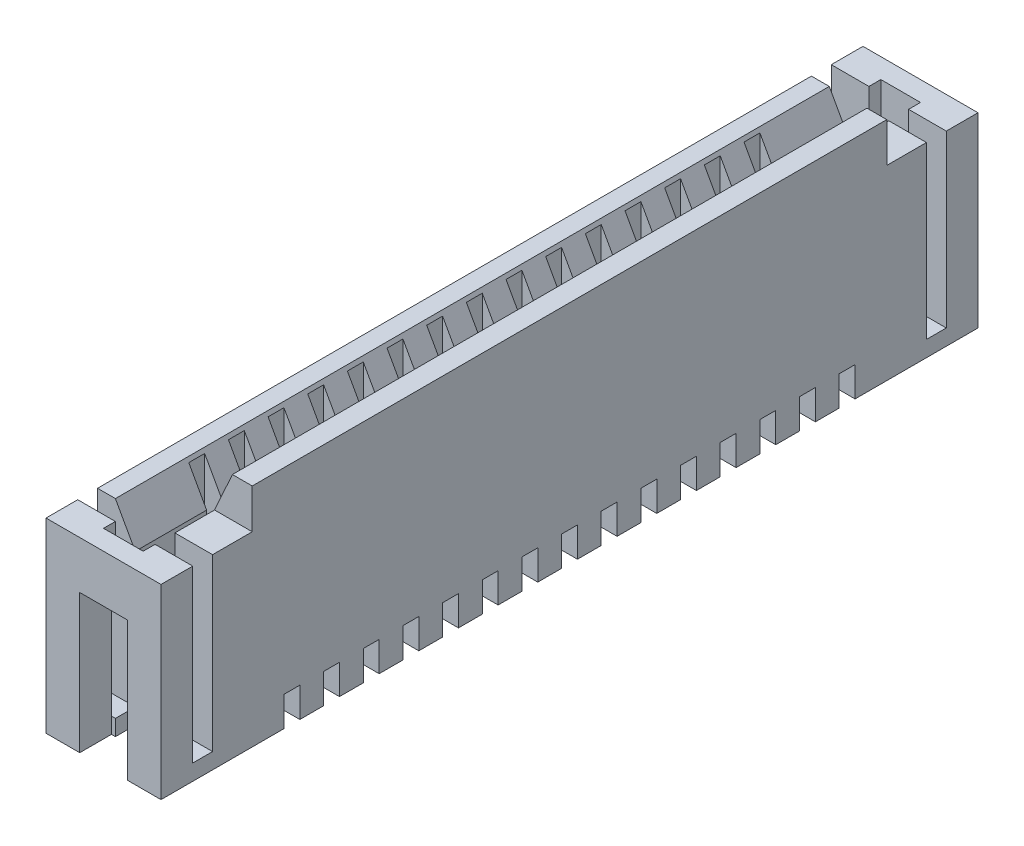
SolidWorks part; units mm, degrees
ref_plane "Plano frontal" through (0, 0, 0) normal (0, 0, 1) x (1, 0, 0)
ref_plane "Plano superior" through (0, 0, 0) normal (0, 1, 0) x (1, 0, 0)
ref_plane "Plano direito" through (0, 0, 0) normal (1, 0, 0) x (0, 0, -1)
sketch "Esboço1" plane through (0, 0, 0) normal (0, 1, 0) x (1, 0, 0)
  line L1 (-1.45, -10.3) -> (1.45, -10.3)
  line L2 (-1.45, -10.3) -> (-1.45, 10.3)
  line L3 (-1.45, 10.3) -> (1.45, 10.3)
  line L4 (1.45, -10.3) -> (1.45, 10.3)
  line L5 (-1.45, -10.3) -> (1.45, 10.3) construction
  line L6 (-1.45, 10.3) -> (1.45, -10.3) construction
  point P0 (0, 0)
  dimension "D1" = 20.6
  dimension "D2" = 2.9
extrude "Ressalto-extrusão1" add sketch "Esboço1" along normal blind 4.7
sketch "Esboço2" plane through (0, 4.7, 0) normal (0, 1, 0) x (1, 0, 0)
  line L1 (-0.5, -9.8) -> (0.5, -9.8)
  line L2 (-0.5, -9.8) -> (-0.5, 9.8)
  line L3 (-0.5, 9.8) -> (0.5, 9.8)
  line L4 (0.5, -9.8) -> (0.5, 9.8)
  line L5 (-0.5, -9.8) -> (0.5, 9.8) construction
  line L6 (-0.5, 9.8) -> (0.5, -9.8) construction
  point P0 (0, 0)
  dimension "D1" = 19.6
  dimension "D2" = 1
extrude "Corte-extrusão1" cut sketch "Esboço2" against normal blind 4.3
sketch "Esboço3" plane through (0, 4.7, 0) normal (0, 1, 0) x (1, 0, 0)
  line L1 (-3.2854, 9.5) -> (3.6069, 9.5)
  line L2 (-3.2854, 9.5) -> (-3.2854, 9)
  line L3 (-3.2854, 9) -> (3.6069, 9)
  line L4 (3.6069, 9.5) -> (3.6069, 9)
  line L5 (-3.2854, -9) -> (4.0468, -9)
  line L6 (-3.2854, -9) -> (-3.2854, -9.5)
  line L7 (-3.2854, -9.5) -> (4.0468, -9.5)
  line L8 (4.0468, -9) -> (4.0468, -9.5)
  dimension "D1" = 9
  dimension "D2" = 9
  dimension "D3" = 0.5
  dimension "D4" = 0.5
extrude "Corte-extrusão2" cut sketch "Esboço3" against normal blind 4.3
chamfer "Chanfro2" distance 0.5 angle 61 1 edges at (-0.5, 4.7, 0)
sketch "Esboço4" plane through (0, 0, 0) normal (0, 0, 1) x (1, 0, 0)
  line L0 (1.45, 4.7) -> (1.45, 5.7)
  line L1 (1.45, 5.7) -> (0.95, 5.7)
  line L2 (0.95, 5.7) -> (0.5, 4.7)
  line L3 (-1.45, 4.7) -> (1.45, 4.7) construction
  line L4 (0.5, 4.7) -> (1.45, 4.7)
  dimension "D1" = 0.95
  dimension "D2" = 1
  dimension "D3" = 0.5
extrude "Ressalto-extrusão2" add sketch "Esboço4" along normal mid plane 16
sketch "Esboço5" plane through (0, 0.4, 0) normal (0, 1, 0) x (1, 0, 0)
  line L0 (0.5, -9) -> (0.5, 9) construction
  line L1 (-0.5, 9.8) -> (0.5, 9.8)
  line L2 (-0.5, 9.8) -> (-0.5, 8.7)
  line L3 (-0.5, 8.7) -> (0.5, 8.7)
  line L4 (0.5, 9.8) -> (0.5, 8.7)
  line L5 (-0.5, 9) -> (-0.5, -9) construction
  line L6 (0.5, -9.8) -> (-0.5, -9.8)
  line L7 (0.5, -9.8) -> (0.5, -8.7)
  line L8 (0.5, -8.7) -> (-0.5, -8.7)
  line L9 (-0.5, -9.8) -> (-0.5, -8.7)
  dimension "D1" = 1.1
  dimension "D2" = 1.1
extrude "Corte-extrusão3" cut sketch "Esboço5" against normal blind 2
sketch "Esboço6" plane through (0, 0.4, 0) normal (0, 1, 0) x (1, 0, 0)
  line L0 (0.5, -8.7) -> (0.5, 8.7) construction
  line L1 (-0.5, 8.7) -> (0.5, 8.7)
  line L2 (-0.5, 8.7) -> (-0.5, 8.3)
  line L3 (-0.5, 8.3) -> (0.5, 8.3)
  line L4 (0.5, 8.7) -> (0.5, 8.3)
  line L5 (-0.5, 8.7) -> (-0.5, -8.7) construction
  line L6 (0.5, -8.7) -> (-0.5, -8.7)
  line L7 (0.5, -8.7) -> (0.5, -8.3)
  line L8 (0.5, -8.3) -> (-0.5, -8.3)
  line L9 (-0.5, -8.7) -> (-0.5, -8.3)
  dimension "D1" = 0.4
  dimension "D2" = 0.4
extrude "Ressalto-extrusão3" add sketch "Esboço6" along normal blind 2
sketch "Esboço7" plane through (0, 4.7, 0) normal (0, 1, 0) x (1, 0, 0)
  line L0 (-1.45, 9) -> (-1.45, -9) construction
  line L1 (-0.95, 0.2) -> (-0.25, 0.2)
  line L2 (-0.95, 0.2) -> (-0.95, -0.2)
  line L3 (-0.95, -0.2) -> (-0.25, -0.2)
  line L4 (-0.25, 0.2) -> (-0.25, -0.2)
  line L5 (1.45, -8) -> (1.45, 8) construction
  line L6 (0.25, 0.2) -> (0.95, 0.2)
  line L7 (0.25, 0.2) -> (0.25, -0.2)
  line L8 (0.25, -0.2) -> (0.95, -0.2)
  line L9 (0.95, 0.2) -> (0.95, -0.2)
  dimension "D1" = 0.7
  dimension "D2" = 0.4
  dimension "D3" = 0.2
  dimension "D4" = 0.5
  dimension "D5" = 0.5
  dimension "D6" = 0.7
extrude "Corte-extrusão4" cut sketch "Esboço7" against normal blind 4.3 and the other way blind 2
sketch "Esboço8" plane through (0, 0, 0) normal (1, 0, 0) x (0, 0, -1)
  line L1 (0.2, -0.25) -> (-0.2, -0.25)
  line L2 (0.2, -0.25) -> (0.2, 0.75)
  line L3 (0.2, 0.75) -> (-0.2, 0.75)
  line L4 (-0.2, -0.25) -> (-0.2, 0.75)
  line L5 (0.2, -0.25) -> (-0.2, 0.75) construction
  line L6 (0.2, 0.75) -> (-0.2, -0.25) construction
  line L7 (10.3, 0) -> (-10.3, 0) construction
  point P0 (0, 0.25)
  dimension "D1" = 0.4
  dimension "D2" = 0
  dimension "D3" = 1
  dimension "D4" = 0.75
extrude "Corte-extrusão7" cut sketch "Esboço8" against normal mid plane 12.1
pattern_linear "Padrão linear1" count 8 spacing 1 along (0, 0, 1) count 8 spacing 1 along (0, 0, -1) of "Corte-extrusão4", "Corte-extrusão7"
sketch "Esboço9" plane through (0, 0, 10.3) normal (0, 0, 1) x (1, 0, 0)
  line L0 (-1.45, 0) -> (1.45, 0) construction
  line L1 (-0.6, 3.5) -> (0.6, 3.5)
  line L2 (-0.6, 3.5) -> (-0.6, -0.9373)
  line L3 (-0.6, -0.9373) -> (0.6, -0.9373)
  line L4 (0.6, 3.5) -> (0.6, -0.9373)
  dimension "D1" = 3.5
  dimension "D2" = 1.2
  dimension "D3" = 0.6
extrude "Corte-extrusão6" cut sketch "Esboço9" against normal blind 0.8
mirror "Espelhar1" about plane through (0, 0, 0) normal (0, 0, 1) of "Corte-extrusão6"
